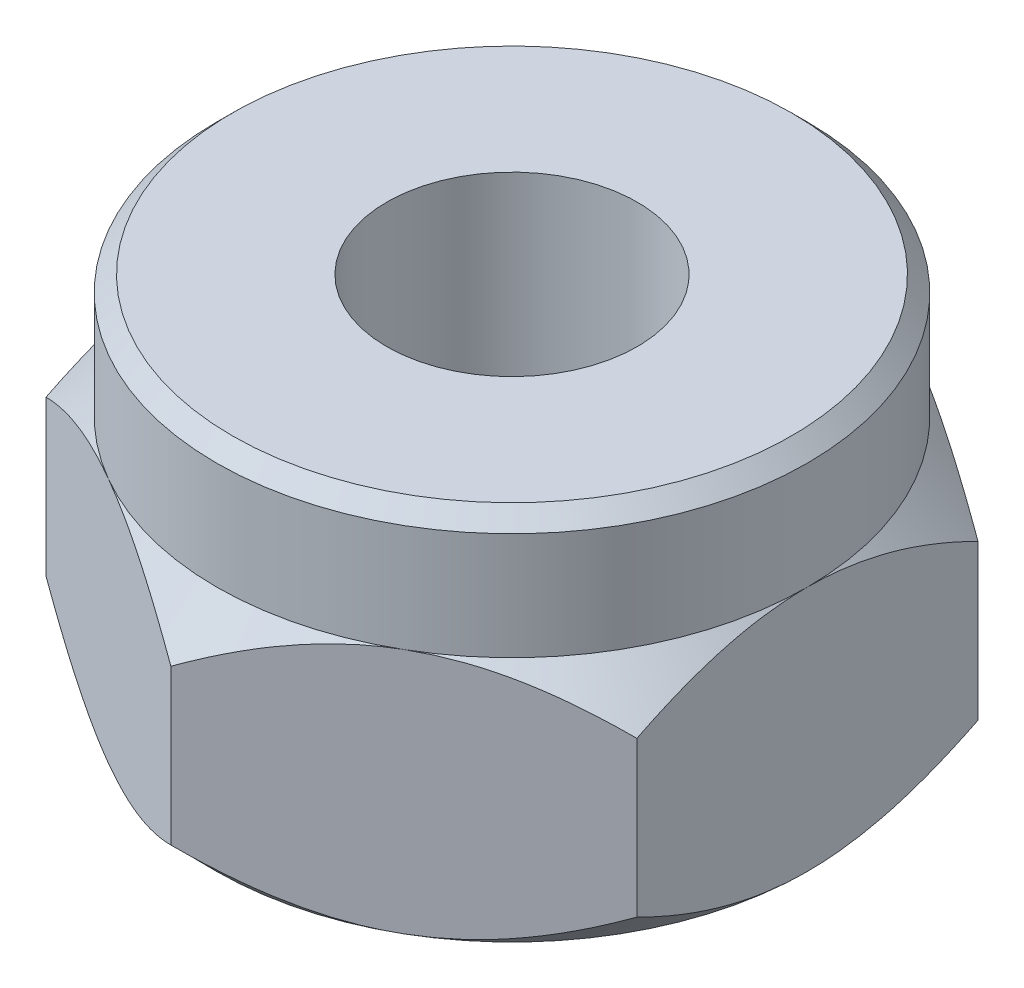
SolidWorks part; units mm, degrees
material "AISI 4130 Steel, normalized at 870C"
ref_plane "Front Plane" through (0, 0, 0) normal (0, 0, 1) x (1, 0, 0)
ref_plane "Top Plane" through (0, 0, 0) normal (0, 1, 0) x (1, 0, 0)
ref_plane "Right Plane" through (0, 0, 0) normal (1, 0, 0) x (0, 0, -1)
sketch "Sketch1" plane through (0, 0, 0) normal (0, 1, 0) x (1, 0, 0)
  line L0 (0, 0) -> (0, 7.5246) construction
  line L1 (0, 5.4993) -> (-4.7625, 2.7496)
  line L2 (-4.7625, 2.7496) -> (-4.7625, -2.7496)
  line L3 (-4.7625, -2.7496) -> (0, -5.4993)
  line L4 (0, -5.4993) -> (4.7625, -2.7496)
  line L5 (4.7625, -2.7496) -> (4.7625, 2.7496)
  line L6 (4.7625, 2.7496) -> (0, 5.4993)
  circle A0 centre (0, 0) radius 4.7625 construction
  dimension "D1" = 9.525
extrude "Extrude1" add sketch "Sketch1" along normal mid plane 3.97
sketch "Sketch2" plane through (0, 1.985, 0) normal (0, 1, 0) x (1, 0, 0)
  line L0 (4.7625, -2.7496) -> (4.7625, 2.7496) construction
  circle A0 centre (0, 0) radius 4.7625
extrude "Extrude3" cut sketch "Sketch2" against normal blind 3.97 draft 45 flip side to cut
mirror "Mirror1" about plane through (0, 0, 0) normal (0, 1, 0) of "Extrude3"
sketch "Sketch3" plane through (0, 1.985, 0) normal (0, 1, 0) x (1, 0, 0)
  circle A0 centre (0, 0) radius 4.7625
  arc A1 (2.3812, -4.1244) -> (4.7625, 0) centre (0, 0) ccw construction
extrude "Extrude4" add sketch "Sketch3" along normal blind 1.9844
hole_wizard "#21 (0.159) Diameter Hole1" positions "Sketch5" profile "Sketch6" hole size "#21" standard "Ansi Inch" end condition through all
sketch "Sketch5" plane through (0, 3.9694, 0) normal (0, 1, 0) x (-1, 0, 0)
  point P0 (0, 0)
sketch "Sketch6" plane through (0, 3.9694, 0) normal (1, 0, 0) x (0, 0, 1)
  line L0 (0, 0) -> (0, 5.9544)
  line L1 (0, 5.9544) -> (2.0193, 5.9544)
  line L2 (2.0193, 5.9544) -> (2.0193, 0)
  line L5 (2.0193, 0) -> (0, 0)
  line L11 (0, -6.35) -> (0, 107.95) construction
  dimension "Thru Hole Dia." = 4.0386
  dimension "Thru Hole Depth" = 5.9544
chamfer "Chamfer1" distance 0.254 angle 45 1 edges at (0, 3.9694, 4.7625)
